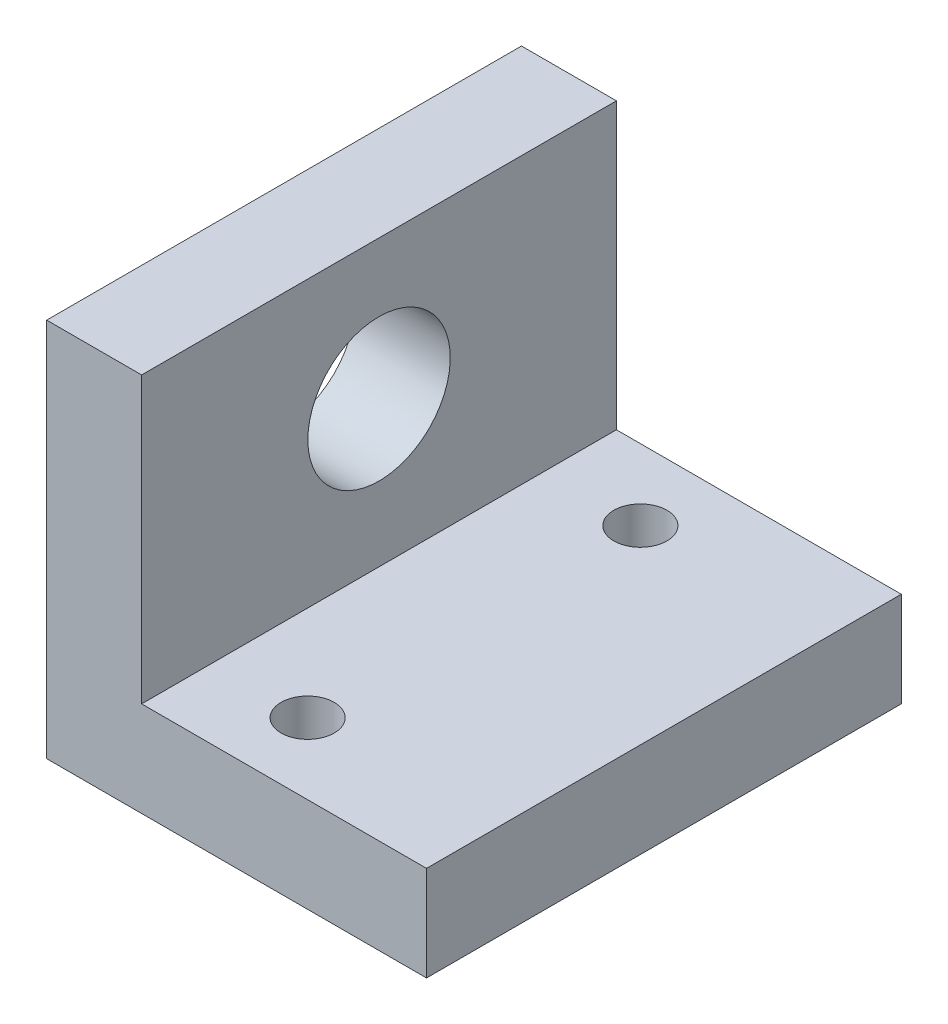
SolidWorks part; units mm, degrees
ref_plane "Front Plane" through (0, 0, 0) normal (0, 0, 1) x (1, 0, 0)
ref_plane "Top Plane" through (0, 0, 0) normal (0, 1, 0) x (1, 0, 0)
ref_plane "Right Plane" through (0, 0, 0) normal (1, 0, 0) x (0, 0, -1)
sketch "Sketch1" plane through (0, 0, 0) normal (0, 0, 1) x (1, 0, 0)
  line L0 (0, 0) -> (0, 25.4)
  line L1 (0, 25.4) -> (6.35, 25.4)
  line L2 (6.35, 25.4) -> (6.35, 6.35)
  line L3 (6.35, 6.35) -> (25.4, 6.35)
  line L4 (25.4, 6.35) -> (25.4, 0)
  line L5 (25.4, 0) -> (0, 0)
  dimension "D1" = 6.35
  dimension "D2" = 6.35
  dimension "D3" = 25.4
  dimension "D4" = 25.4
extrude "Boss-Extrude1" add sketch "Sketch1" against normal blind 31.75
sketch "Sketch2" plane through (0, 0, 0) normal (-1, 0, 0) x (0, 0, 1)
  line L0 (-31.75, 0) -> (0, 0) construction
  circle A0 centre (-15.875, 16.0782) radius 4.7625
  dimension "D1" = 9.525
  dimension "D2" = 16.0782
extrude "Cut-Extrude1" cut sketch "Sketch2" against normal through all
sketch "Sketch3" plane through (0, 6.35, 0) normal (0, 1, 0) x (1, 0, 0)
  line L0 (25.4, 31.75) -> (6.35, 31.75) construction
  line L1 (25.4, 0) -> (6.35, 0) construction
  line L2 (25.4, 31.75) -> (25.4, 0) construction
  circle A0 centre (12.7, 27.0002) radius 1.778
  circle A1 centre (12.7, 4.7498) radius 1.778
  dimension "D1" = 3.556
  dimension "D2" = 3.556
  dimension "D4" = 4.7498
  dimension "D3" = 4.7498
  dimension "D5" = 12.7
  dimension "D6" = 12.7
extrude "Cut-Extrude2" cut sketch "Sketch3" against normal through all
